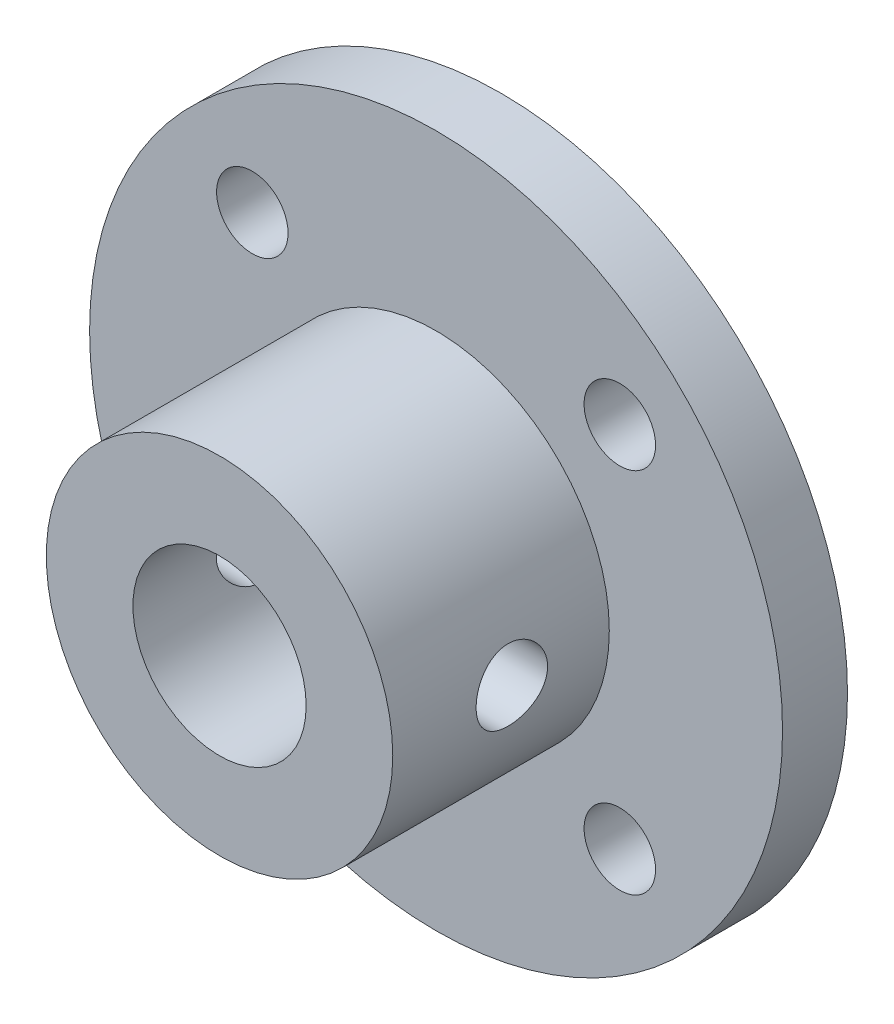
SolidWorks part; units mm, degrees
ref_plane "前视基准面" through (0, 0, 0) normal (0, 0, 1) x (1, 0, 0)
ref_plane "上视基准面" through (0, 0, 0) normal (0, 1, 0) x (1, 0, 0)
ref_plane "右视基准面" through (0, 0, 0) normal (1, 0, 0) x (0, 0, -1)
sketch "草图1" plane through (0, 0, 0) normal (0, 0, 1) x (1, 0, 0)
  circle A0 centre (0, 0) radius 16
  dimension "D1" = 32
extrude "凸台-拉伸1" add sketch "草图1" along normal blind 3
sketch "草图2" plane through (0, 0, 3) normal (0, 0, 1) x (1, 0, 0)
  circle A0 centre (0, 0) radius 8
  dimension "D1" = 16
extrude "凸台-拉伸2" add sketch "草图2" along normal blind 10
sketch "草图3" plane through (0, 0, 13) normal (0, 0, 1) x (1, 0, 0)
  circle A0 centre (0, 0) radius 4
  dimension "D1" = 8
extrude "切除-拉伸1" cut sketch "草图3" against normal through all
sketch "草图5" plane through (0, 0, 3) normal (0, 0, 1) x (1, 0, 0)
  line L1 (8.4853, -8.4853) -> (-8.4853, -8.4853) construction
  line L2 (8.4853, -8.4853) -> (8.4853, 8.4853) construction
  line L3 (8.4853, 8.4853) -> (-8.4853, 8.4853) construction
  line L4 (-8.4853, -8.4853) -> (-8.4853, 8.4853) construction
  line L5 (8.4853, -8.4853) -> (-8.4853, 8.4853) construction
  line L6 (8.4853, 8.4853) -> (-8.4853, -8.4853) construction
  circle A0 centre (-8.4853, -8.4853) radius 1.5
  circle A1 centre (-8.4853, 8.4853) radius 1.5
  circle A2 centre (8.4853, -8.4853) radius 1.5
  circle A3 centre (8.4853, 8.4853) radius 1.5
  point P0 (0, 0)
  dimension "D1" = 3
  dimension "D2" = 24
extrude "切除-拉伸3" cut sketch "草图5" against normal through all
hole_wizard "M4 螺纹孔1" positions "3D草图1" profile "草图6" tap size "M4" standard "GB" end condition up to next
sketch3d "3D草图1"
  line L0 (-8.4853, 8.4853, 0) -> (-8.4853, 8.4853, 3) construction
  line L1 (8.4853, 8.4853, 0) -> (8.4853, 8.4853, 3) construction
  line L2 (8.4853, -8.4853, 0) -> (8.4853, -8.4853, 3) construction
  line L3 (-8.4853, -8.4853, 0) -> (-8.4853, -8.4853, 3) construction
  point P0 (-8.4853, 8.4853, 3)
  point P4 (8.4853, 8.4853, 3)
  point P8 (8.4853, -8.4853, 3)
  point P12 (-8.4853, -8.4853, 3)
sketch "草图6" plane through (-8.4853, 8.4853, 3) normal (1, 0, 0) x (0, -1, 0)
  line L0 (0, 0) -> (0, 3)
  line L1 (0, 3) -> (1.65, 3)
  line L2 (1.65, 3) -> (1.65, 0)
  line L5 (1.65, 0) -> (0, 0)
  line L11 (0, -6.35) -> (0, 107.95) construction
  dimension "通孔螺纹孔钻头直径" = 3.3
  dimension "通孔螺纹孔钻头深度" = 3
cosmetic thread "孔螺蚊线1" parameters "D2"=4
cosmetic thread "孔螺蚊线2" parameters "D2"=4
cosmetic thread "孔螺蚊线3" parameters "D2"=4
cosmetic thread "孔螺蚊线4" parameters "D2"=4
hole_wizard "M4 螺纹孔2" positions "3D草图2" profile "草图7" tap size "M4" standard "GB" end condition through all
sketch3d "3D草图2"
  point P0 (8, 0, 7.5)
  dimension "D1" = 7.5
sketch "草图7" plane through (8, 0, 7.5) normal (0, 1, 0) x (0, 0, -1)
  line L0 (0, 0) -> (0, 24)
  line L1 (0, 24) -> (1.65, 24)
  line L2 (1.65, 24) -> (1.65, 0)
  line L5 (1.65, 0) -> (0, 0)
  line L11 (0, -6.35) -> (0, 107.95) construction
  dimension "通孔螺纹孔钻头直径" = 3.3
  dimension "通孔螺纹孔钻头深度" = 24
cosmetic thread "孔螺蚊线8" parameters "D2"=4
sketch "草图8" plane through (0, 0, 0) normal (0, 0, -1) x (-1, 0, 0)
